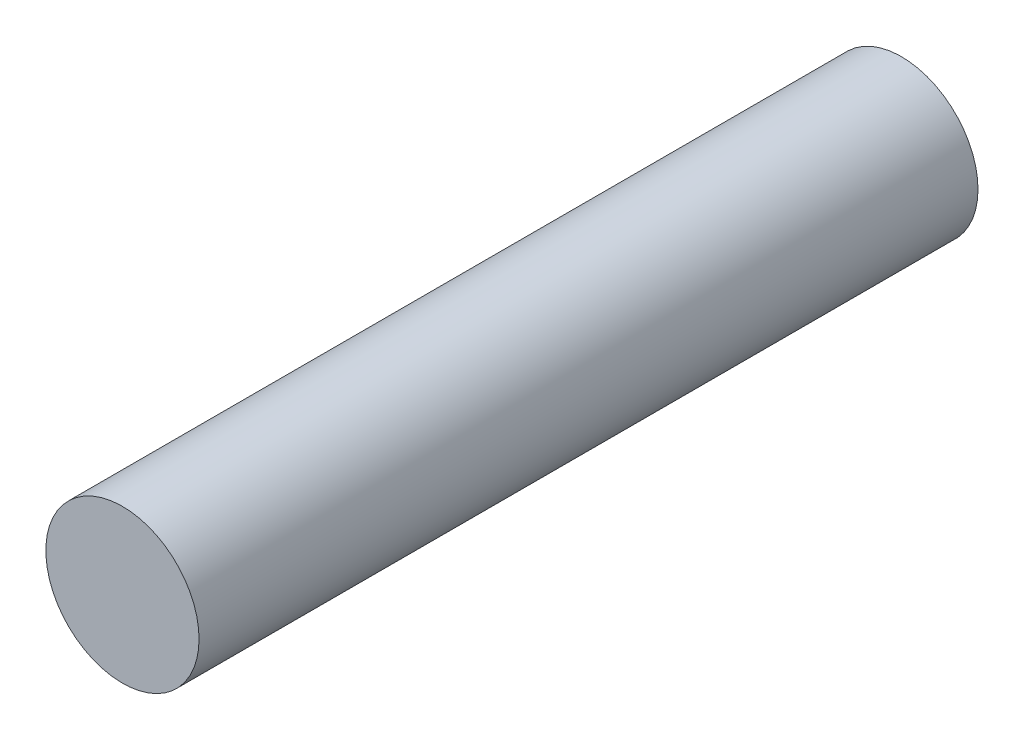
SolidWorks part; units mm, degrees
ref_plane "Front Plane" through (0, 0, 0) normal (0, 0, 1) x (1, 0, 0)
ref_plane "Top Plane" through (0, 0, 0) normal (0, 1, 0) x (1, 0, 0)
ref_plane "Right Plane" through (0, 0, 0) normal (1, 0, 0) x (0, 0, -1)
sketch "Sketch1" plane through (0, 0, 0) normal (0, 0, 1) x (1, 0, 0)
  circle A0 centre (0, 0) radius 2.95
  dimension "D1" = 5.9
extrude "Boss-Extrude1" add sketch "Sketch1" along normal blind 30
sketch "Sketch2" plane through (0, 0, 0) normal (0, 0, -1) x (-1, 0, 0)
  line L0 (-1.6194, 1.4) -> (1.6194, 1.4)
  arc A0 (-1.6194, 1.4) -> (1.6194, 1.4) centre (0, 0) ccw
  dimension "D1" = 1.4
extrude "Cut-Extrude1" cut sketch "Sketch2" against normal blind 7
